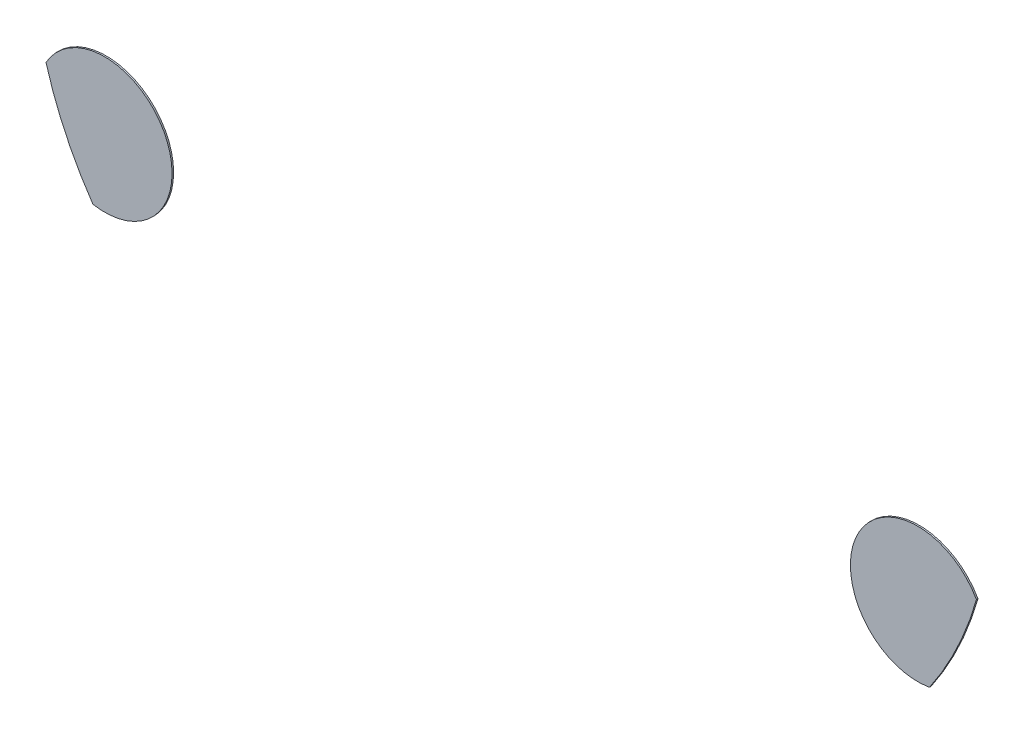
SolidWorks part; units mm, degrees
ref_plane "Alzado" through (0, 0, 0) normal (0, 0, 1) x (1, 0, 0)
ref_plane "Planta" through (0, 0, 0) normal (0, 1, 0) x (1, 0, 0)
ref_plane "Vista lateral" through (0, 0, 0) normal (1, 0, 0) x (0, 0, -1)
sketch "Model" plane through (0, 0, 0) normal (0, 0, 1) x (1, 0, 0)
  arc A0 (3.8902, 33.5205) -> (6.9184, 27.1073) centre (25.0717, 39.6007) ccw
  arc A1 (60.8938, 27.1073) -> (63.9221, 33.5205) centre (42.7406, 39.6007) ccw
  arc A2 (6.9184, 27.1073) -> (3.8902, 33.5205) centre (7.677, 31.387) ccw
  arc A3 (63.9221, 33.5205) -> (60.8938, 27.1073) centre (60.1353, 31.387) ccw
extrude "Saliente-Extruir1" add sketch "Model" along normal blind 0.1
